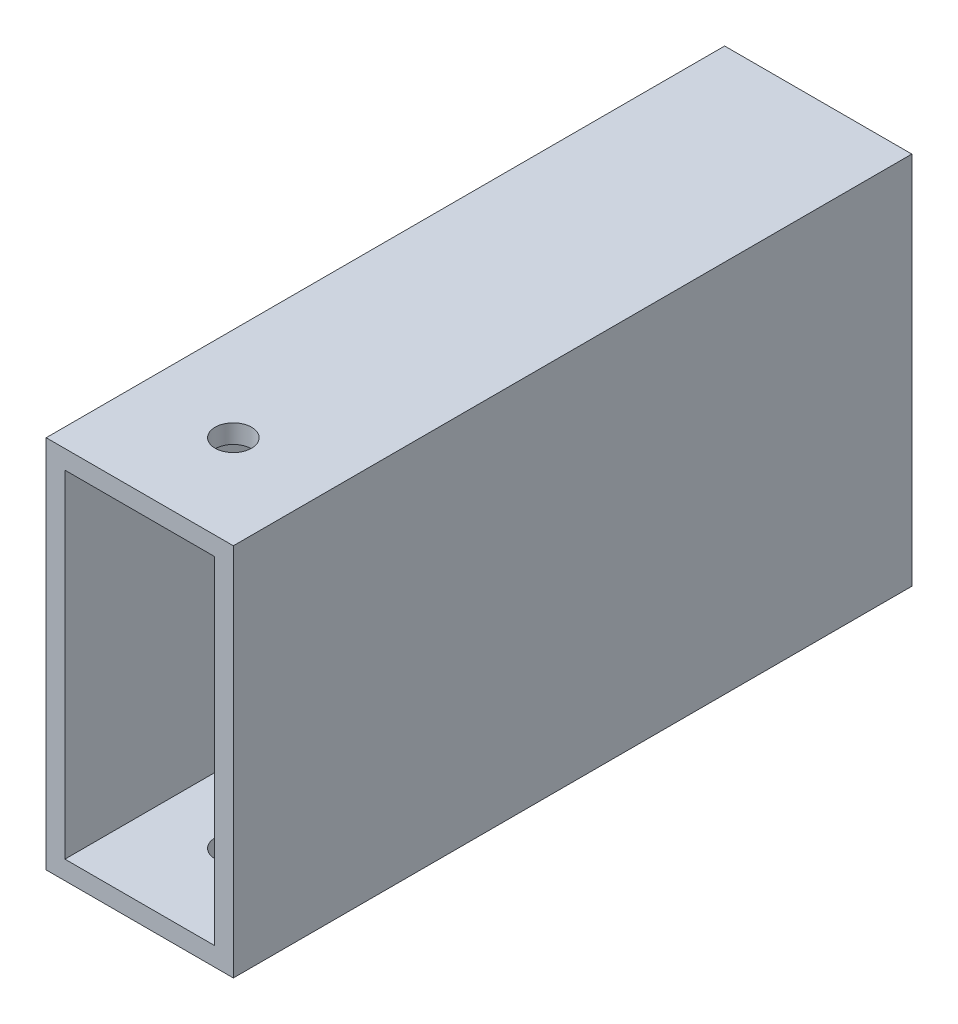
SolidWorks part; units mm, degrees
ref_plane "Front Plane" through (0, 0, 0) normal (0, 0, 1) x (1, 0, 0)
ref_plane "Top Plane" through (0, 0, 0) normal (0, 1, 0) x (1, 0, 0)
ref_plane "Right Plane" through (0, 0, 0) normal (1, 0, 0) x (0, 0, -1)
sketch "Sketch1" plane through (0, 0, 0) normal (0, 0, 1) x (1, 0, 0)
  line L1 (-12.7, -25.4) -> (12.7, -25.4)
  line L2 (-12.7, -25.4) -> (-12.7, 25.4)
  line L3 (-12.7, 25.4) -> (12.7, 25.4)
  line L4 (12.7, -25.4) -> (12.7, 25.4)
  line L5 (-12.7, -25.4) -> (12.7, 25.4) construction
  line L6 (-12.7, 25.4) -> (12.7, -25.4) construction
  point P0 (0, 0)
  dimension "D1" = 25.4
  dimension "D2" = 50.8
extrude "Extrude-Thin1" add sketch "Sketch1" along normal mid plane 92.075 thin thin type one direction reverse wall 2.54
sketch "Sketch2" plane through (0, -25.4, 0) normal (0, -1, 0) x (1, 0, 0)
  circle A0 centre (0, 33.3375) radius 2.4765
extrude "Cut-Extrude1" cut sketch "Sketch2" against normal through all
